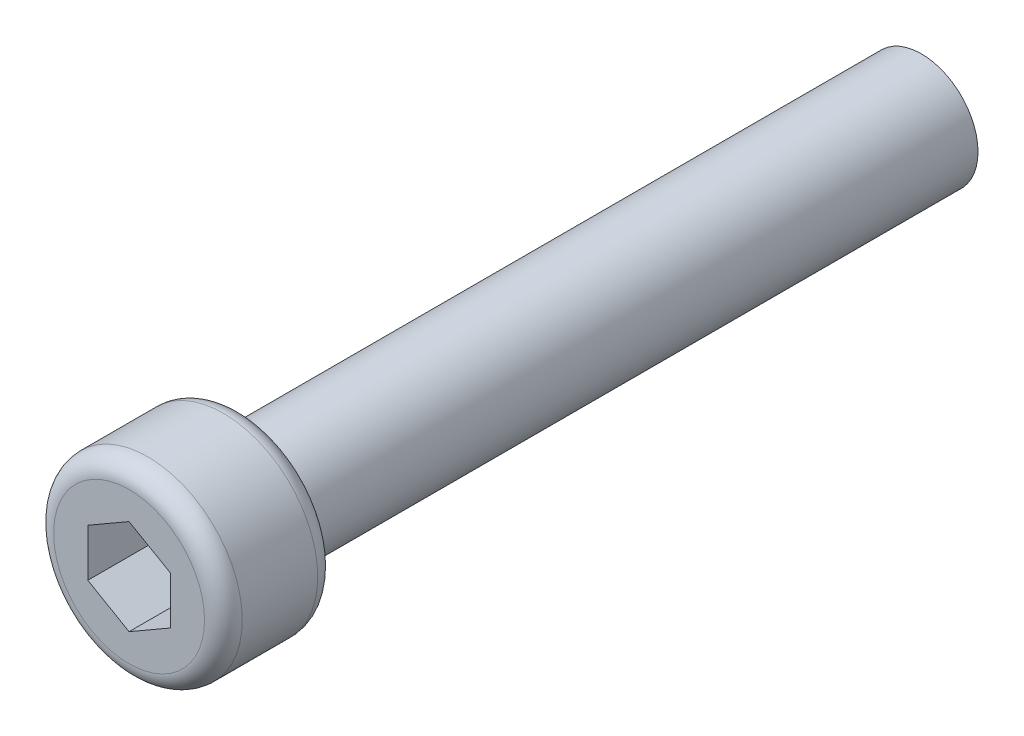
SolidWorks part; units mm, degrees
ref_plane "Front Plane" through (0, 0, 0) normal (0, 0, 1) x (1, 0, 0)
ref_plane "Top Plane" through (0, 0, 0) normal (0, 1, 0) x (1, 0, 0)
ref_plane "Right Plane" through (0, 0, 0) normal (1, 0, 0) x (0, 0, -1)
sketch "Sketch1" plane through (0, 0, 0) normal (0, 0, 1) x (1, 0, 0)
  circle A1 centre (0, 1.5842) radius 1.5
extrude "Boss-Extrude1" add sketch "Sketch1" against normal blind 18
sketch "Sketch2" plane through (0, 0, 0) normal (0, 0, 1) x (1, 0, 0)
  circle A0 centre (0, 1.5842) radius 2.5
extrude "Boss-Extrude2" add sketch "Sketch2" along normal blind 3
fillet "Fillet1" radius 0.5 2 edges at (2.5, 1.5842, 3) (2.5, 1.5842, 0)
sketch "Sketch3" plane through (0, 0, 3) normal (0, 0, 1) x (1, 0, 0)
  line L1 (0, 0.3207) -> (1.0942, 0.9524)
  line L2 (1.0942, 0.9524) -> (1.0942, 2.2159)
  line L3 (1.0942, 2.2159) -> (0, 2.8477)
  line L4 (0, 2.8477) -> (-1.0942, 2.2159)
  line L5 (-1.0942, 2.2159) -> (-1.0942, 0.9524)
  line L6 (-1.0942, 0.9524) -> (0, 0.3207)
  circle A0 centre (0, 1.5842) radius 1.0942 construction
extrude "Cut-Extrude1" cut sketch "Sketch3" against normal blind 2
